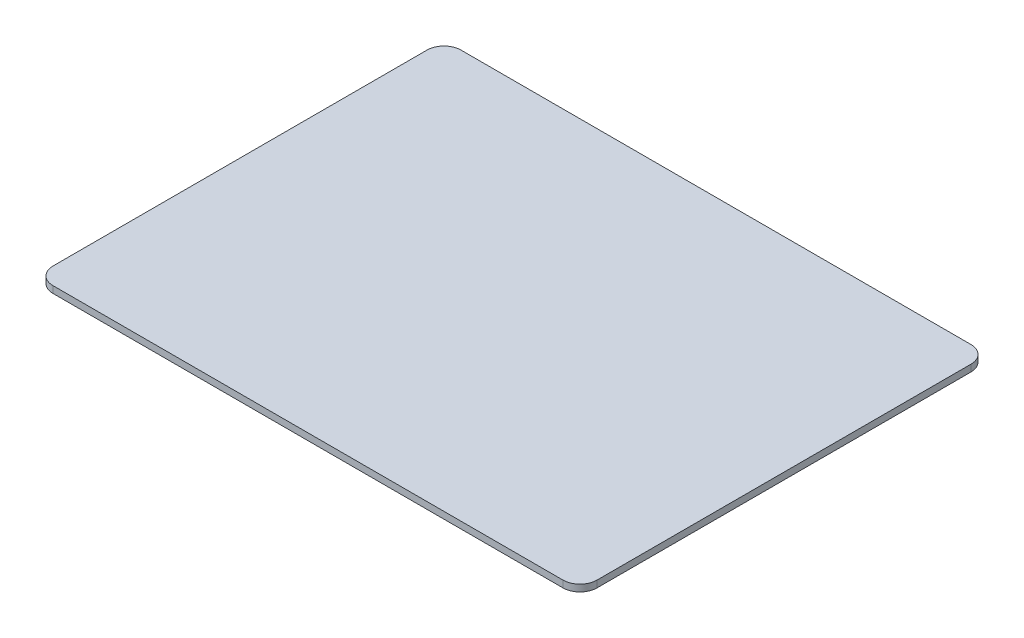
SolidWorks part; units mm, degrees
ref_plane "Front Plane" through (0, 0, 0) normal (0, 0, 1) x (1, 0, 0)
ref_plane "Top Plane" through (0, 0, 0) normal (0, 1, 0) x (1, 0, 0)
ref_plane "Right Plane" through (0, 0, 0) normal (1, 0, 0) x (0, 0, -1)
sketch "Sketch2" plane through (0, 0, 0) normal (0, 1, 0) x (1, 0, 0)
  line L1 (10, 0) -> (310, 0)
  line L2 (0, 10) -> (0, 230)
  line L3 (10, 240) -> (310, 240)
  line L4 (320, 10) -> (320, 230)
  arc A0 (10, 0) -> (0, 10) centre (10, 10) cw
  arc A1 (310, 0) -> (320, 10) centre (310, 10) ccw
  arc A2 (310, 240) -> (320, 230) centre (310, 230) cw
  arc A3 (0, 230) -> (10, 240) centre (10, 230) cw
  point P7 (0, 0)
  point P12 (320, 240)
  point P15 (0, 240)
  dimension "D3" = 10
  dimension "D4" = 10
  dimension "D1" = 240
  dimension "D2" = 320
extrude "Boss-Extrude1" add sketch "Sketch2" along normal blind 4
sketch "Sketch3" plane through (0, 4, 0) normal (0, 1, 0) x (1, 0, 0)
  circle A0 centre (23.8114, 218.6324) radius 1.5
  dimension "D1" = 3
